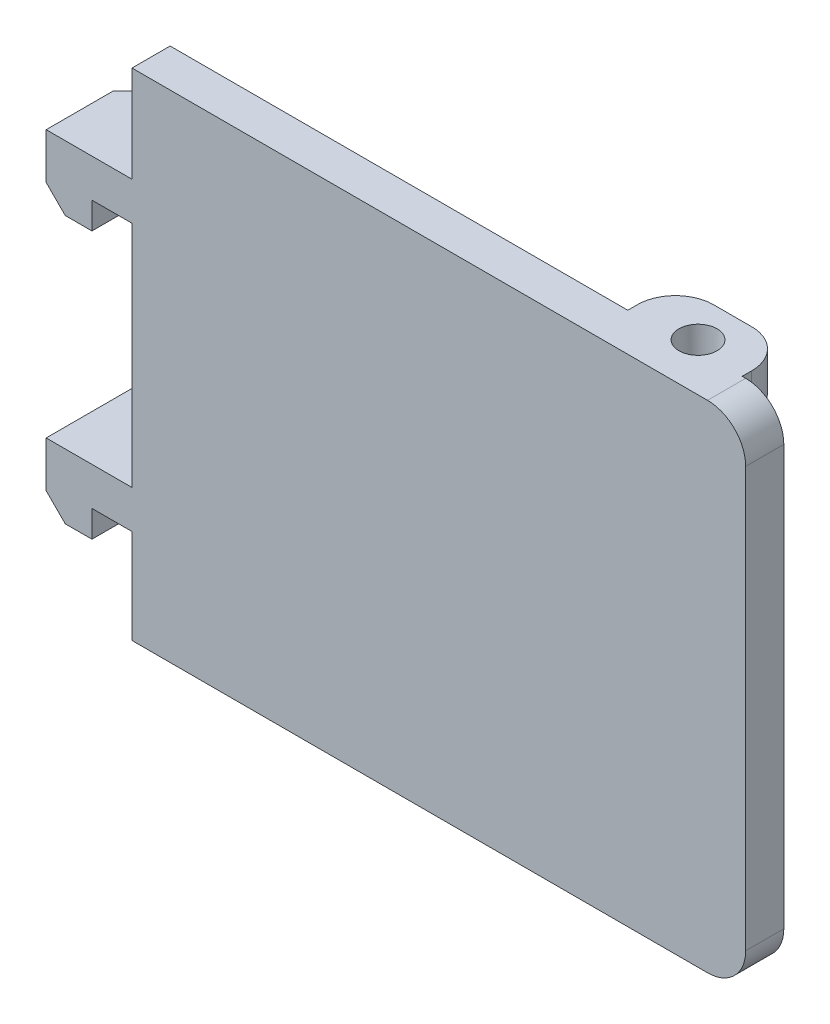
SolidWorks part; units mm, degrees
ref_plane "前视基准面" through (0, 0, 0) normal (0, 0, 1) x (1, 0, 0)
ref_plane "上视基准面" through (0, 0, 0) normal (0, 1, 0) x (1, 0, 0)
ref_plane "右视基准面" through (0, 0, 0) normal (1, 0, 0) x (0, 0, -1)
other "Configuration Table"
sketch "草图2" plane through (0, 0, 0) normal (0, 0, 1) x (1, 0, 0)
  line L1 (15.1907, -6.4342) -> (-16.9928, -6.4342)
  line L2 (15.1907, -6.4342) -> (15.1907, -32.4342)
  line L3 (15.1907, -32.4342) -> (-16.9928, -32.4342)
  line L4 (-16.9928, -6.4342) -> (-16.9928, -32.4342)
  line L6 (13.1907, -6.4342) -> (-12.8093, -6.4342) construction
  dimension "D1" = 32.1835
  dimension "D2" = 26
extrude "凸台-拉伸1" add sketch "草图2" along normal blind 2
fillet "圆角1" radius 2 2 edges at (15.1907, -32.4342, 1) (15.1907, -6.4342, 1)
sketch "草图5" plane through (0, 0, 0) normal (0, 0, -1) x (-1, 0, 0)
  line L1 (-13.0072, -6.4342) -> (-7.0072, -6.4342)
  line L2 (-13.0072, -6.4342) -> (-13.0072, -8.4342)
  line L3 (-13.0072, -8.4342) -> (-7.0072, -8.4342)
  line L4 (-7.0072, -6.4342) -> (-7.0072, -8.4342)
  line L5 (16.9928, -32.4342) -> (-13.1907, -32.4342) construction
  line L6 (-13.0072, -32.4342) -> (-7.0072, -32.4342)
  line L7 (-13.0072, -32.4342) -> (-13.0072, -30.4342)
  line L8 (-13.0072, -30.4342) -> (-7.0072, -30.4342)
  line L9 (-7.0072, -32.4342) -> (-7.0072, -30.4342)
  line L11 (16.9928, -6.4342) -> (16.9928, -32.4342) construction
  line L12 (-13.1907, -6.4342) -> (16.9928, -6.4342) construction
  dimension "D1" = 2
  dimension "D2" = 24
  dimension "D3" = 6
extrude "凸台-拉伸2" add sketch "草图5" along normal blind 2.5
fillet "圆角2" radius 2 4 edges at (7.0072, -7.4342, -2.5) (13.0072, -7.4342, -2.5) (7.0072, -31.4342, -2.5) (13.0072, -31.4342, -2.5)
sketch "草图6" plane through (0, -32.4342, 0) normal (0, -1, 0) x (1, 0, 0)
  line L1 (17.1907, 2) -> (17.1907, -8) construction
  line L2 (-16.9928, 2) -> (13.1907, 2) construction
  circle A0 centre (10.1907, -0.5) radius 1
  dimension "D1" = 2
  dimension "D2" = 7
  dimension "D3" = 2.5
extrude "切除-拉伸3" cut sketch "草图6" against normal blind 4 draft 2
sketch "草图7" plane through (0, -6.4342, 0) normal (0, 1, 0) x (1, 0, 0)
  circle A0 centre (10.1907, 0.5) radius 1
  arc A1 (10.9751, 0) -> (9.4064, 0) centre (10.1907, 0.5) ccw construction
extrude "切除-拉伸4" cut sketch "草图7" against normal blind 4 draft 2
sketch "草图9" plane through (0, 0, 0) normal (0, 0, -1) x (-1, 0, 0)
  line L0 (16.9928, -6.4342) -> (16.9928, -32.4342) construction
  line L1 (16.9928, -11.4842) -> (21.4928, -11.4842)
  line L2 (16.9928, -11.4842) -> (16.9928, -13.4842)
  line L3 (16.9928, -13.4842) -> (21.4928, -13.4842)
  line L4 (21.4928, -11.4842) -> (21.4928, -13.4842)
  line L5 (16.9928, -32.4342) -> (-7.0072, -32.4342) construction
  line L6 (16.9928, -25.4842) -> (21.4928, -25.4842)
  line L7 (16.9928, -25.4842) -> (16.9928, -27.4842)
  line L8 (16.9928, -27.4842) -> (21.4928, -27.4842)
  line L9 (21.4928, -25.4842) -> (21.4928, -27.4842)
  dimension "D1" = 4.95
  dimension "D2" = 18.95
  dimension "D3" = 4.5
  dimension "D4" = 2
extrude "凸台-拉伸3" add sketch "草图9" against normal blind 2
sketch "草图10" plane through (0, 0, 0) normal (0, 0, -1) x (-1, 0, 0)
  line L1 (21.4928, -13.4842) -> (19.0928, -13.4842)
  line L2 (21.4928, -13.4842) -> (21.4928, -14.8842)
  line L3 (21.4928, -14.8842) -> (19.0928, -14.8842)
  line L4 (19.0928, -13.4842) -> (19.0928, -14.8842)
  line L5 (21.4928, -27.4842) -> (19.0928, -27.4842)
  line L6 (21.4928, -27.4842) -> (21.4928, -28.8842)
  line L7 (21.4928, -28.8842) -> (19.0928, -28.8842)
  line L8 (19.0928, -27.4842) -> (19.0928, -28.8842)
  point P10 (0, 0)
  dimension "D1" = 2.4
  dimension "D2" = 1.4
extrude "凸台-拉伸4" add sketch "草图10" against normal blind 2
chamfer "倒角1" distance 1 angle 45 2 edges at (-21.4928, -28.8842, 1) (-21.4928, -14.8842, 1)
sketch "草图11" plane through (0, 0, 0) normal (0, 0, -1) x (-1, 0, 0)
  line L0 (16.9928, -6.4342) -> (16.9928, -11.4842) construction
  line L1 (21.4928, -11.4842) -> (12.9928, -11.4842)
  line L2 (21.4928, -11.4842) -> (21.4928, -13.4842)
  line L3 (21.4928, -13.4842) -> (12.9928, -13.4842)
  line L4 (12.9928, -11.4842) -> (12.9928, -13.4842)
  line L5 (21.4928, -25.4842) -> (12.9928, -25.4842)
  line L6 (21.4928, -25.4842) -> (21.4928, -27.4842)
  line L7 (21.4928, -27.4842) -> (12.9928, -27.4842)
  line L8 (12.9928, -25.4842) -> (12.9928, -27.4842)
  point P10 (0, 0)
  point P11 (0, 0)
  point P13 (0, 0)
  dimension "D1" = 4
extrude "凸台-拉伸5" add sketch "草图11" along normal blind 2.5
chamfer "倒角2" distance 1 angle 45 3 edges at (-21.4928, -12.4842, -2.5) (-12.9928, -26.4842, -2.5) (-12.9928, -12.4842, -2.5)
